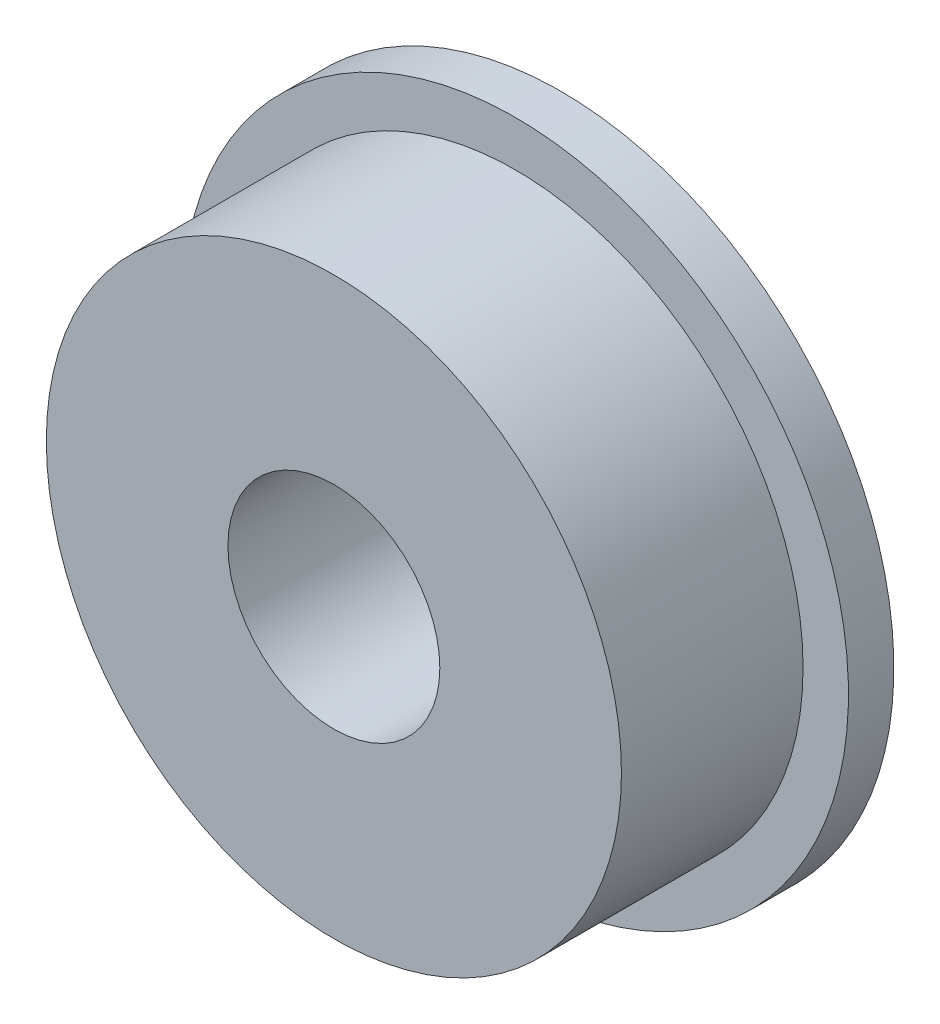
SolidWorks part; units mm, degrees
ref_plane "前基準面" through (0, 0, 0) normal (0, 0, 1) x (1, 0, 0)
ref_plane "上基準面" through (0, 0, 0) normal (0, 1, 0) x (1, 0, 0)
ref_plane "右基準面" through (0, 0, 0) normal (1, 0, 0) x (0, 0, -1)
sketch "草圖1" plane through (0, 0, 0) normal (0, 0, 1) x (1, 0, 0)
  circle A0 centre (0, 0) radius 3.5
  circle A1 centre (0, 0) radius 9.5
  dimension "D1" = 7
  dimension "D2" = 19
extrude "填料-伸長1" add sketch "草圖1" along normal blind 6
sketch "草圖2" plane through (0, 0, 0) normal (0, 0, -1) x (-1, 0, 0)
  circle A0 centre (0, 0) radius 11
  circle A1 centre (0, 0) radius 3.5
  dimension "D1" = 22
  dimension "D2" = 7
extrude "填料-伸長2" add sketch "草圖2" along normal blind 1.5
